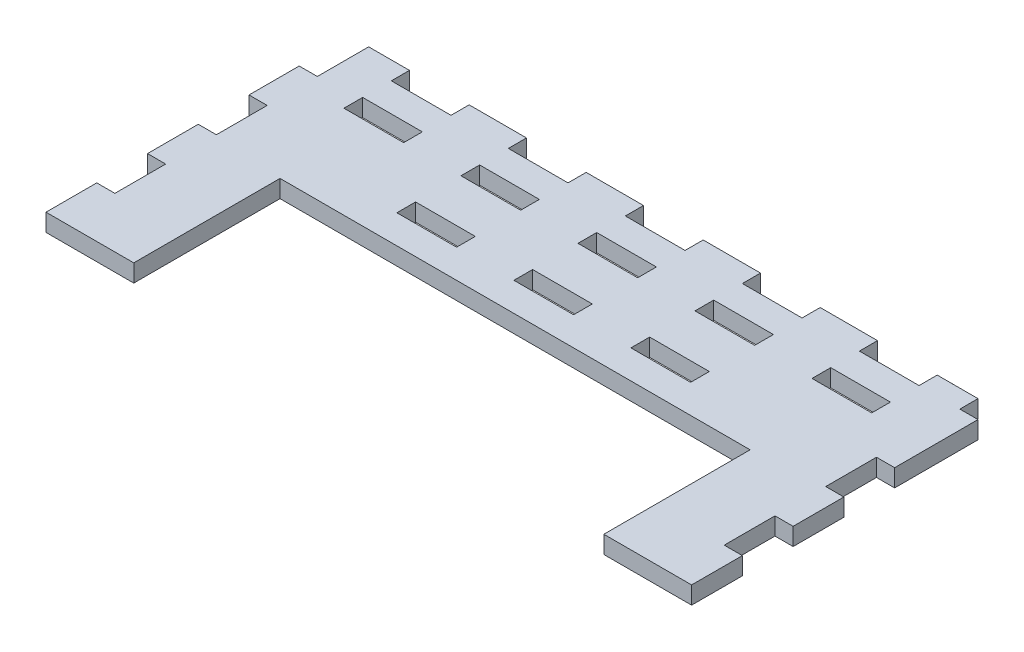
SolidWorks part; units mm, degrees
ref_plane "Front Plane" through (0, 0, 0) normal (0, 0, 1) x (1, 0, 0)
ref_plane "Top Plane" through (0, 0, 0) normal (0, 1, 0) x (1, 0, 0)
ref_plane "Right Plane" through (0, 0, 0) normal (1, 0, 0) x (0, 0, -1)
sketch "Sketch1" plane through (0, 0, 0) normal (0, 1, 0) x (1, 0, 0)
  line L0 (95.3444, 0) -> (95.3444, 25)
  line L1 (0, 0) -> (110.3444, 0) construction
  line L2 (0, 0) -> (0, 52.05)
  line L3 (0, 52.05) -> (110.3444, 52.05)
  line L4 (110.3444, 0) -> (110.3444, 52.05)
  line L5 (95.3444, 25) -> (15, 25)
  line L6 (15, 25) -> (15, 0)
  line L7 (55.1722, 0) -> (55.1722, 25) construction
  line L8 (110.3444, 0) -> (95.3444, 0)
  line L9 (15, 0) -> (0, 0)
  line L10 (0, 25) -> (110.3444, 25) construction
  dimension "D1" = 15
extrude "Boss-Extrude1" add sketch "Sketch1" along normal up to vertex (3 mm away)
sketch "Sketch2" plane through (0, 0, 0) normal (0, 1, 0) x (1, 0, 0)
  line L4 (3.1, 17.35) -> (-0.1, 17.35)
  line L5 (3.1, 8.675) -> (3.1, 17.35)
  line L6 (-0.1, 8.675) -> (3.1, 8.675)
  line L7 (-0.1, 17.35) -> (-0.1, 8.675)
  line L8 (3.1, 17.35) -> (-0.1, 17.35)
  line L9 (3.1, 8.675) -> (3.1, 17.35)
  line L10 (-0.1, 8.675) -> (3.1, 8.675)
  line L11 (-0.1, 17.35) -> (-0.1, 8.675)
  line L12 (3.1, 34.7) -> (-0.1, 34.7)
  line L13 (3.1, 26.025) -> (3.1, 34.7)
  line L14 (-0.1, 26.025) -> (3.1, 26.025)
  line L15 (-0.1, 34.7) -> (-0.1, 26.025)
  line L16 (3.1, 34.7) -> (-0.1, 34.7)
  line L17 (3.1, 26.025) -> (3.1, 34.7)
  line L18 (-0.1, 26.025) -> (3.1, 26.025)
  line L19 (-0.1, 34.7) -> (-0.1, 26.025)
  line L20 (3.1, 52.15) -> (-0.1, 52.15)
  line L21 (3.1, 43.275) -> (3.1, 52.15)
  line L22 (-0.1, 43.275) -> (3.1, 43.275)
  line L23 (-0.1, 52.15) -> (-0.1, 43.275)
  line L24 (3.1, 52.15) -> (-0.1, 52.15)
  line L25 (3.1, 43.275) -> (3.1, 52.15)
  line L26 (-0.1, 43.275) -> (3.1, 43.275)
  line L27 (-0.1, 52.15) -> (-0.1, 43.275)
  line L28 (40.2722, 52.15) -> (30.0722, 52.15)
  line L29 (40.2722, 48.95) -> (40.2722, 52.15)
  line L30 (30.0722, 48.95) -> (40.2722, 48.95)
  line L31 (30.0722, 52.15) -> (30.0722, 48.95)
  line L32 (40.2722, 52.15) -> (30.0722, 52.15)
  line L33 (40.2722, 48.95) -> (40.2722, 52.15)
  line L34 (30.0722, 48.95) -> (40.2722, 48.95)
  line L35 (30.0722, 52.15) -> (30.0722, 48.95)
  line L36 (60.2722, 33.1) -> (50.0722, 33.1)
  line L37 (60.2722, 29.9) -> (60.2722, 33.1)
  line L38 (50.0722, 29.9) -> (60.2722, 29.9)
  line L39 (50.0722, 33.1) -> (50.0722, 29.9)
  line L40 (60.2722, 33.1) -> (50.0722, 33.1)
  line L41 (60.2722, 29.9) -> (60.2722, 33.1)
  line L42 (50.0722, 29.9) -> (60.2722, 29.9)
  line L43 (50.0722, 33.1) -> (50.0722, 29.9)
  line L44 (60.2722, 44.05) -> (50.0722, 44.05)
  line L45 (60.2722, 40.85) -> (60.2722, 44.05)
  line L46 (50.0722, 40.85) -> (60.2722, 40.85)
  line L47 (50.0722, 44.05) -> (50.0722, 40.85)
  line L48 (60.2722, 44.05) -> (50.0722, 44.05)
  line L49 (60.2722, 40.85) -> (60.2722, 44.05)
  line L50 (50.0722, 40.85) -> (60.2722, 40.85)
  line L51 (50.0722, 44.05) -> (50.0722, 40.85)
  line L52 (60.2722, 52.15) -> (50.0722, 52.15)
  line L53 (50.0722, 52.15) -> (50.0722, 48.95)
  line L54 (50.0722, 48.95) -> (60.2722, 48.95)
  line L55 (60.2722, 48.95) -> (60.2722, 52.15)
  line L56 (60.2722, 52.15) -> (50.0722, 52.15)
  line L57 (50.0722, 52.15) -> (50.0722, 48.95)
  line L58 (50.0722, 48.95) -> (60.2722, 48.95)
  line L59 (60.2722, 48.95) -> (60.2722, 52.15)
  line L60 (20.2722, 44.05) -> (10.0722, 44.05)
  line L61 (20.2722, 40.85) -> (20.2722, 44.05)
  line L62 (10.0722, 40.85) -> (20.2722, 40.85)
  line L63 (10.0722, 44.05) -> (10.0722, 40.85)
  line L64 (20.2722, 44.05) -> (10.0722, 44.05)
  line L65 (20.2722, 40.85) -> (20.2722, 44.05)
  line L66 (10.0722, 40.85) -> (20.2722, 40.85)
  line L67 (10.0722, 44.05) -> (10.0722, 40.85)
  line L68 (20.2722, 52.15) -> (10.0722, 52.15)
  line L69 (20.2722, 48.95) -> (20.2722, 52.15)
  line L70 (10.0722, 48.95) -> (20.2722, 48.95)
  line L71 (10.0722, 52.15) -> (10.0722, 48.95)
  line L72 (20.2722, 52.15) -> (10.0722, 52.15)
  line L73 (20.2722, 48.95) -> (20.2722, 52.15)
  line L74 (10.0722, 48.95) -> (20.2722, 48.95)
  line L75 (10.0722, 52.15) -> (10.0722, 48.95)
  line L76 (40.2722, 33.1) -> (30.0722, 33.1)
  line L77 (40.2722, 29.9) -> (40.2722, 33.1)
  line L78 (30.0722, 29.9) -> (40.2722, 29.9)
  line L79 (30.0722, 33.1) -> (30.0722, 29.9)
  line L80 (40.2722, 33.1) -> (30.0722, 33.1)
  line L81 (40.2722, 29.9) -> (40.2722, 33.1)
  line L82 (30.0722, 29.9) -> (40.2722, 29.9)
  line L83 (30.0722, 33.1) -> (30.0722, 29.9)
  line L84 (40.2722, 44.05) -> (30.0722, 44.05)
  line L85 (30.0722, 44.05) -> (30.0722, 40.85)
  line L86 (30.0722, 40.85) -> (40.2722, 40.85)
  line L87 (40.2722, 40.85) -> (40.2722, 44.05)
  line L88 (40.2722, 44.05) -> (30.0722, 44.05)
  line L89 (30.0722, 44.05) -> (30.0722, 40.85)
  line L90 (30.0722, 40.85) -> (40.2722, 40.85)
  line L91 (40.2722, 40.85) -> (40.2722, 44.05)
  line L92 (110.4444, 17.35) -> (107.2444, 17.35)
  line L93 (107.2444, 17.35) -> (107.2444, 8.675)
  line L94 (107.2444, 8.675) -> (110.4444, 8.675)
  line L95 (110.4444, 8.675) -> (110.4444, 17.35)
  line L96 (110.4444, 17.35) -> (107.2444, 17.35)
  line L97 (107.2444, 17.35) -> (107.2444, 8.675)
  line L98 (107.2444, 8.675) -> (110.4444, 8.675)
  line L99 (110.4444, 8.675) -> (110.4444, 17.35)
  line L100 (100.2722, 40.85) -> (100.2722, 44.05)
  line L101 (90.0722, 40.85) -> (100.2722, 40.85)
  line L102 (90.0722, 44.05) -> (90.0722, 40.85)
  line L103 (100.2722, 44.05) -> (90.0722, 44.05)
  line L104 (100.2722, 40.85) -> (100.2722, 44.05)
  line L105 (90.0722, 40.85) -> (100.2722, 40.85)
  line L106 (90.0722, 44.05) -> (90.0722, 40.85)
  line L107 (100.2722, 44.05) -> (90.0722, 44.05)
  line L108 (100.2722, 48.95) -> (100.2722, 52.15)
  line L109 (90.0722, 48.95) -> (100.2722, 48.95)
  line L110 (90.0722, 52.15) -> (90.0722, 48.95)
  line L111 (100.2722, 52.15) -> (90.0722, 52.15)
  line L112 (100.2722, 48.95) -> (100.2722, 52.15)
  line L113 (90.0722, 48.95) -> (100.2722, 48.95)
  line L114 (90.0722, 52.15) -> (90.0722, 48.95)
  line L115 (100.2722, 52.15) -> (90.0722, 52.15)
  line L116 (110.4444, 34.7) -> (107.2444, 34.7)
  line L117 (107.2444, 34.7) -> (107.2444, 26.025)
  line L118 (107.2444, 26.025) -> (110.4444, 26.025)
  line L119 (110.4444, 26.025) -> (110.4444, 34.7)
  line L120 (110.4444, 34.7) -> (107.2444, 34.7)
  line L121 (107.2444, 34.7) -> (107.2444, 26.025)
  line L122 (107.2444, 26.025) -> (110.4444, 26.025)
  line L123 (110.4444, 26.025) -> (110.4444, 34.7)
  line L124 (80.2722, 48.95) -> (80.2722, 52.15)
  line L125 (70.0722, 48.95) -> (80.2722, 48.95)
  line L126 (70.0722, 52.15) -> (70.0722, 48.95)
  line L127 (80.2722, 52.15) -> (70.0722, 52.15)
  line L128 (80.2722, 48.95) -> (80.2722, 52.15)
  line L129 (70.0722, 48.95) -> (80.2722, 48.95)
  line L130 (70.0722, 52.15) -> (70.0722, 48.95)
  line L131 (80.2722, 52.15) -> (70.0722, 52.15)
  line L132 (80.2722, 40.85) -> (80.2722, 44.05)
  line L133 (70.0722, 40.85) -> (80.2722, 40.85)
  line L134 (70.0722, 44.05) -> (70.0722, 40.85)
  line L135 (80.2722, 44.05) -> (70.0722, 44.05)
  line L136 (80.2722, 40.85) -> (80.2722, 44.05)
  line L137 (70.0722, 40.85) -> (80.2722, 40.85)
  line L138 (70.0722, 44.05) -> (70.0722, 40.85)
  line L139 (80.2722, 44.05) -> (70.0722, 44.05)
  line L140 (80.2722, 29.9) -> (80.2722, 33.1)
  line L141 (70.0722, 29.9) -> (80.2722, 29.9)
  line L142 (70.0722, 33.1) -> (70.0722, 29.9)
  line L143 (80.2722, 33.1) -> (70.0722, 33.1)
  line L144 (80.2722, 29.9) -> (80.2722, 33.1)
  line L145 (70.0722, 29.9) -> (80.2722, 29.9)
  line L146 (70.0722, 33.1) -> (70.0722, 29.9)
  line L147 (80.2722, 33.1) -> (70.0722, 33.1)
  line L148 (107.2444, 52.15) -> (107.2444, 48.95)
  line L149 (110.4444, 52.15) -> (107.2444, 52.15)
  line L150 (110.4444, 48.95) -> (110.4444, 52.15)
  line L151 (107.2444, 48.95) -> (110.4444, 48.95)
  line L152 (107.2444, 52.15) -> (107.2444, 48.95)
  line L153 (110.4444, 52.15) -> (107.2444, 52.15)
  line L154 (110.4444, 48.95) -> (110.4444, 52.15)
  line L155 (107.2444, 48.95) -> (110.4444, 48.95)
  dimension "D1" = 0
  dimension "D2" = 0
  dimension "D3" = 0
  dimension "D4" = 0
  dimension "D5" = 0
  dimension "D6" = 0
  dimension "D7" = 0
  dimension "D8" = 0
  dimension "D9" = 0
  dimension "D10" = 0
  dimension "D11" = 0
  dimension "D12" = 0
  dimension "D13" = 0
  dimension "D14" = 0
  dimension "D15" = 0
  dimension "D16" = 0
  dimension "D17" = 0
  dimension "D18" = 0
  dimension "D19" = 0
extrude "Cut-Extrude1" cut sketch "Sketch2" along normal through all
